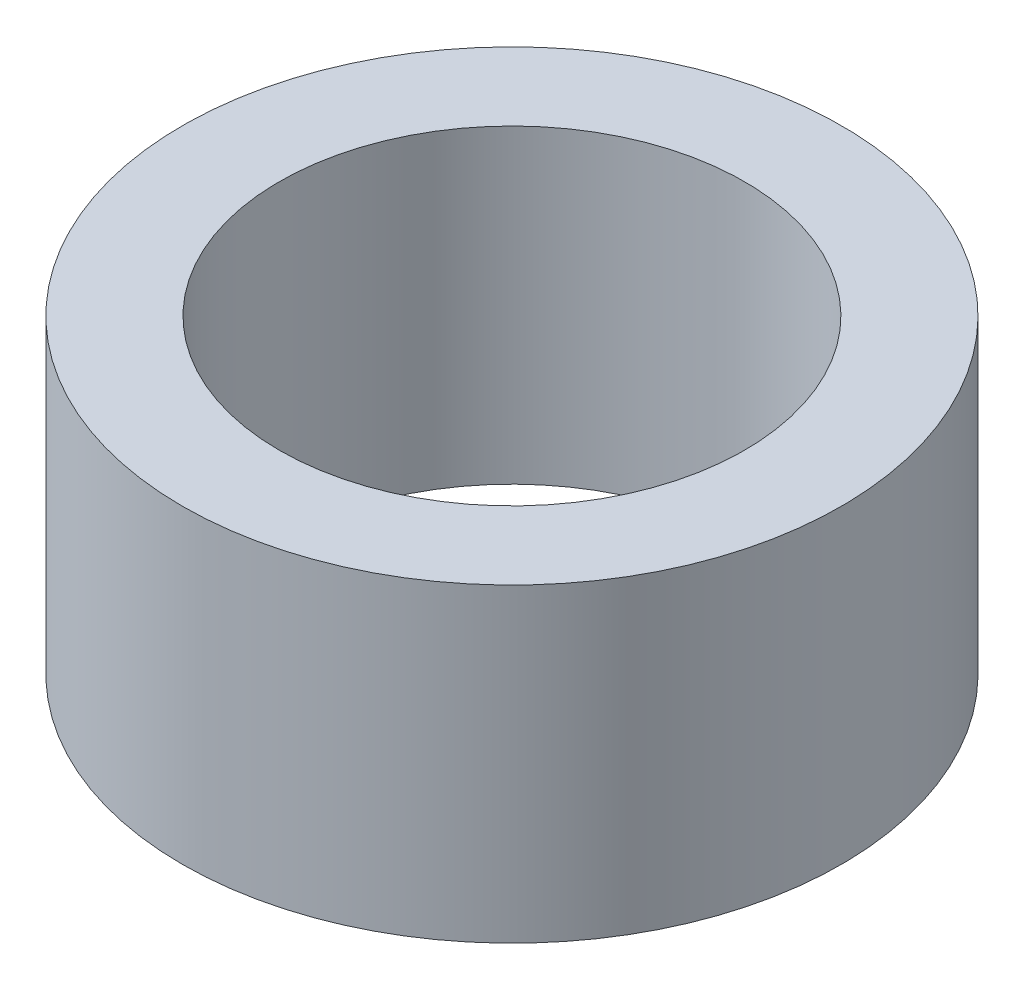
SolidWorks part; units mm, degrees
ref_plane "Front Plane" through (0, 0, 0) normal (0, 0, 1) x (1, 0, 0)
ref_plane "Top Plane" through (0, 0, 0) normal (0, 1, 0) x (1, 0, 0)
ref_plane "Right Plane" through (0, 0, 0) normal (1, 0, 0) x (0, 0, -1)
sketch "Sketch1" plane through (0, 0, 0) normal (0, 1, 0) x (1, 0, 0)
  circle A0 centre (0, 0) radius 42.5
  circle A1 centre (0, 0) radius 30
  dimension "D1" = 85
  dimension "D2" = 60
extrude "Boss-Extrude1" add sketch "Sketch1" along normal blind 40
